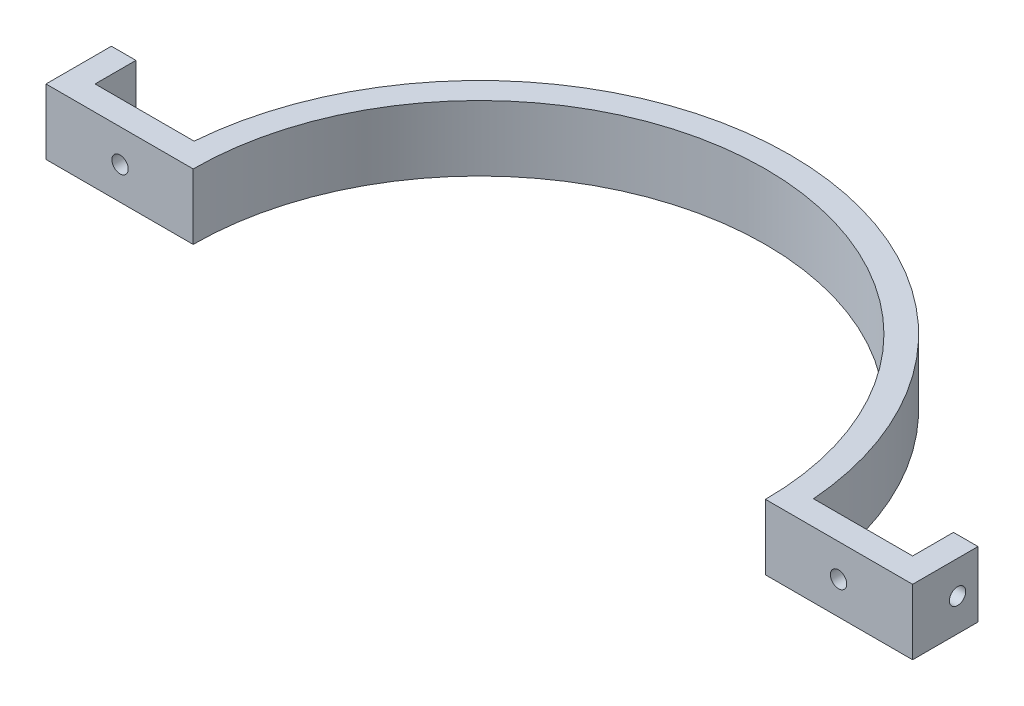
SolidWorks part; units mm, degrees
ref_plane "Front Plane" through (0, 0, 0) normal (0, 0, 1) x (1, 0, 0)
ref_plane "Top Plane" through (0, 0, 0) normal (0, 1, 0) x (1, 0, 0)
ref_plane "Right Plane" through (0, 0, 0) normal (1, 0, 0) x (0, 0, -1)
sketch "Sketch1" plane through (0, 0, 0) normal (0, 1, 0) x (1, 0, 0)
  line L0 (-55.5625, 0) -> (-84.1375, 0)
  line L2 (-79.375, 4.7625) -> (-60.1367, 4.7625)
  line L3 (0, 0) -> (0, 89.1254) construction
  line L7 (-84.1375, 0) -> (-84.1375, 12.7)
  line L8 (-84.1375, 12.7) -> (-79.375, 12.7)
  line L9 (-79.375, 12.7) -> (-79.375, 4.7625)
  line L10 (79.375, 4.7625) -> (60.1367, 4.7625)
  line L11 (55.5625, 0) -> (84.1375, 0)
  line L12 (79.375, 12.7) -> (79.375, 4.7625)
  line L13 (84.1375, 12.7) -> (79.375, 12.7)
  line L14 (84.1375, 0) -> (84.1375, 12.7)
  arc A0 (-55.5625, 0) -> (55.5625, 0) centre (0, 0) cw
  arc A1 (-60.1367, 4.7625) -> (60.1367, 4.7625) centre (0, 0) cw
  dimension "D1" = 55.5625
  dimension "D5" = 60.325
  dimension "D2" = 28.575
  dimension "D3" = 12.7
  dimension "D4" = 4.7625
  dimension "D6" = 4.7625
extrude "Boss-Extrude1" add sketch "Sketch1" along normal blind 12.7
sketch "Sketch5" plane through (0, 0, -4.7625) normal (0, 0, -1) x (-1, 0, 0)
  line L0 (60.1367, 6.35) -> (79.375, 6.35) construction
  line L5 (60.1367, 12.7) -> (60.1367, 0) construction
  line L6 (79.375, 12.7) -> (79.375, 0) construction
  circle A2 centre (69.7559, 6.35) radius 1.5875
  dimension "D1" = 3.175
extrude "Cut-Extrude1" cut sketch "Sketch5" against normal through all
sketch "Sketch6" plane through (-79.375, 0, 0) normal (1, 0, 0) x (0, 0, -1)
  line L0 (8.7312, 0) -> (8.7312, 12.7) construction
  line L1 (4.7625, 0) -> (12.7, 0) construction
  line L2 (4.7625, 12.7) -> (12.7, 12.7) construction
  circle A0 centre (8.7312, 6.35) radius 1.5875
  dimension "D1" = 3.175
extrude "Cut-Extrude2" cut sketch "Sketch6" against normal through all
mirror "Mirror2" about plane through (0, 0, 0) normal (1, 0, 0) of "Cut-Extrude1", "Cut-Extrude2"
mirror "Mirror1" [suppressed] about plane through (0, 0, 0) normal (1, 0, 0)
